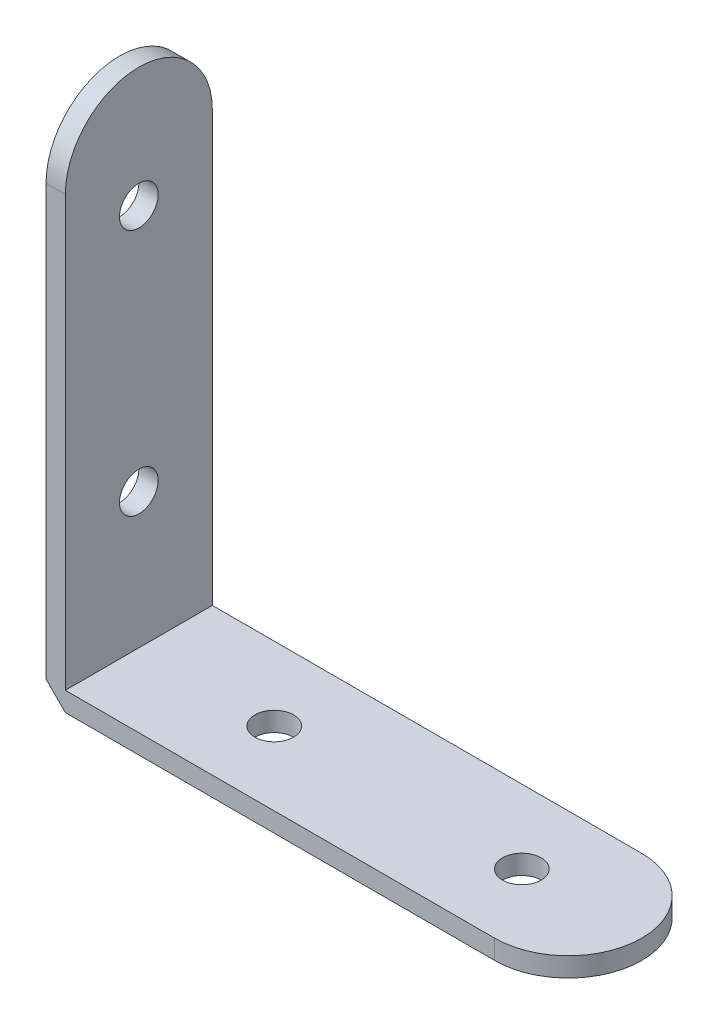
SolidWorks part; units mm, degrees
ref_plane "前视基准面" through (0, 0, 0) normal (0, 0, 1) x (1, 0, 0)
ref_plane "上视基准面" through (0, 0, 0) normal (0, 1, 0) x (1, 0, 0)
ref_plane "右视基准面" through (0, 0, 0) normal (1, 0, 0) x (0, 0, -1)
sketch "草图1" plane through (0, 0, 0) normal (0, 1, 0) x (1, 0, 0)
  line L1 (23, -9.5) -> (-32.5, -9.5)
  line L3 (23, 9.5) -> (-32.5, 9.5)
  line L4 (-32.5, -9.5) -> (-32.5, 9.5)
  arc A2 (23, -9.5) -> (23, 9.5) centre (23, 0) ccw
  circle A4 centre (-15, 0) radius 2.5
  circle A5 centre (17, 0) radius 2.5
  point P0 (0, 0)
  dimension "D3" = 5
  dimension "D2" = 9.5
  dimension "D4" = 5
  dimension "D5" = 32
  dimension "D6" = 17.5
  dimension "D1" = 19
extrude "凸台-拉伸1" add sketch "草图1" along normal blind 2.5
sketch "草图2" plane through (0, 0, 9.5) normal (0, 0, 1) x (1, 0, 0)
  line L0 (-35, 2.5) -> (-32.5, 0)
  line L2 (-32.5, 2.5) -> (-32.5, 67.5)
  line L3 (-32.5, 67.5) -> (-35, 67.5)
  line L4 (-35, 2.5) -> (-35, 67.5)
  line L5 (-32.5, 2.5) -> (-32.5, 0)
  dimension "D1" = 65
  dimension "D2" = 2.5
extrude "凸台-拉伸2" add sketch "草图2" against normal blind 19
sketch "草图3" plane through (-32.5, 0, 0) normal (1, 0, 0) x (0, 0, -1)
  line L2 (-9.5, 67.5) -> (9.5, 67.5)
  line L3 (-9.5, 67.5) -> (-9.5, 58)
  line L5 (9.5, 67.5) -> (9.5, 58)
  arc A2 (9.5, 58) -> (-9.5, 58) centre (0, 58) ccw
  line M3 (9.5, 2.5) -> (9.5, 67.5)
  line M4 (9.5, 67.5) -> (-9.5, 67.5)
  line M5 (-9.5, 67.5) -> (-9.5, 2.5)
extrude "切除-拉伸1" cut sketch "草图3" against normal blind 19 contours A2 M3 M4 | A2 L2 M5
sketch "草图4" plane through (-32.5, 0, 0) normal (1, 0, 0) x (0, 0, -1)
  line L0 (9.5, 2.5) -> (-9.5, 2.5) construction
  circle A0 centre (0, 52) radius 2.5
  circle A1 centre (0, 20) radius 2.5
  dimension "D1" = 5
  dimension "D2" = 5
  dimension "D3" = 32
  dimension "D4" = 17.5
extrude "切除-拉伸2" cut sketch "草图4" against normal blind 19
